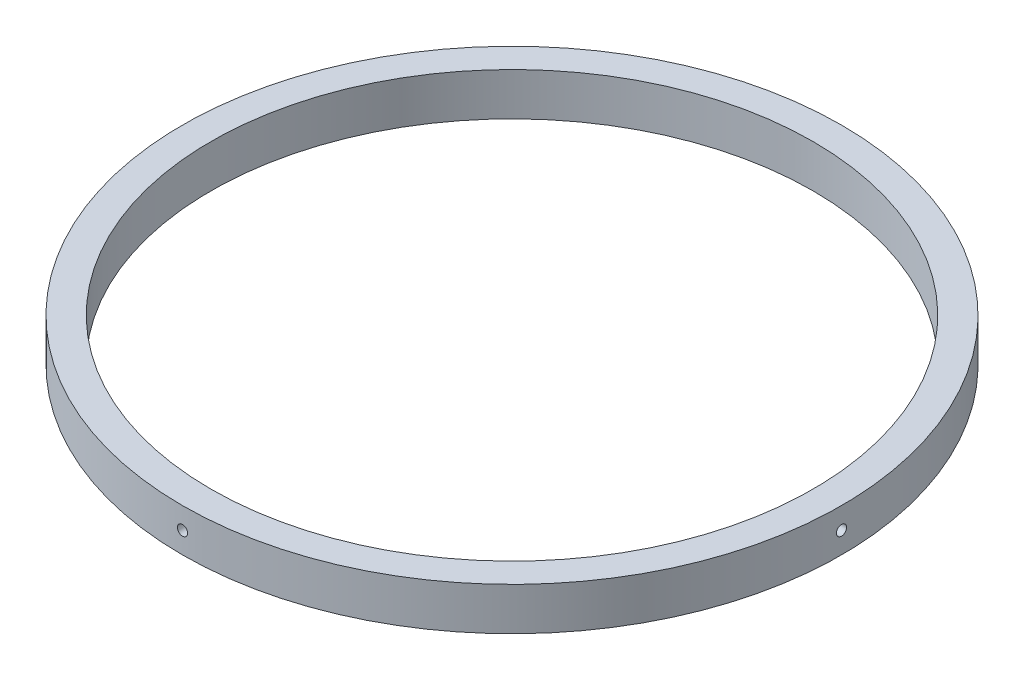
SolidWorks part; units mm, degrees
ref_plane "Front Plane" through (0, 0, 0) normal (0, 0, 1) x (1, 0, 0)
ref_plane "Top Plane" through (0, 0, 0) normal (0, 1, 0) x (1, 0, 0)
ref_plane "Right Plane" through (0, 0, 0) normal (1, 0, 0) x (0, 0, -1)
sketch "Sketch1" plane through (0, 0, 0) normal (0, 1, 0) x (1, 0, 0)
  circle A0 centre (0, 0) radius 73.4441
  circle A1 centre (0, 0) radius 67.0941
  dimension "D1" = 146.8882
  dimension "D2" = 134.1882
extrude "Boss-Extrude1" add sketch "Sketch1" along normal blind 9.525
ref_plane "Plane1" through (0, 0, 73.4441) normal (0, 0, 1) x (1, 0, 0)
sketch "Sketch2" plane through (0, 0, 73.4441) normal (0, 0, 1) x (1, 0, 0)
  line L0 (0, 0) -> (0, 9.525) construction
  line L1 (73.4441, 9.525) -> (-73.4441, 9.525) construction
  point P5 (0, 4.7625)
hole_wizard "Tap Drill for #4-40 Tap1" positions "Sketch2" profile "Sketch3" hole size "#4-40" standard "ANSI Inch"
sketch "Sketch3" plane through (0, 4.7625, 73.4441) normal (1, 0, 0) x (0, -1, 0)
  line L0 (0, 0) -> (0, 5.4417)
  line L1 (0, 5.4417) -> (1.1303, 4.7625)
  line L2 (1.1303, 4.7625) -> (1.1303, 0)
  line L5 (1.1303, 0) -> (0, 0)
  line L10 (0, 5.4417) -> (-1.1303, 4.7625) construction
  line L11 (0, -6.35) -> (0, 107.95) construction
  dimension "Hole Dia." = 2.2606
  dimension "Hole Depth" = 4.7625
  dimension "Drill Angle" = 118
pattern_circular "CirPattern1" count 4 every 90 about axis through (0, 9.525, 0) along (0, 1, 0) of "Tap Drill for #4-40 Tap1"
equation "\"OD\" = 5.783"
equation "\"ID\"= \"OD\" - 0.5"
equation "\"thk\"= 3 / 8"
equation "\"D1@Sketch1\"=\"OD\""
equation "\"D2@Sketch1\"=\"ID\""
equation "\"D1@Boss-Extrude1\"=\"thk\""
